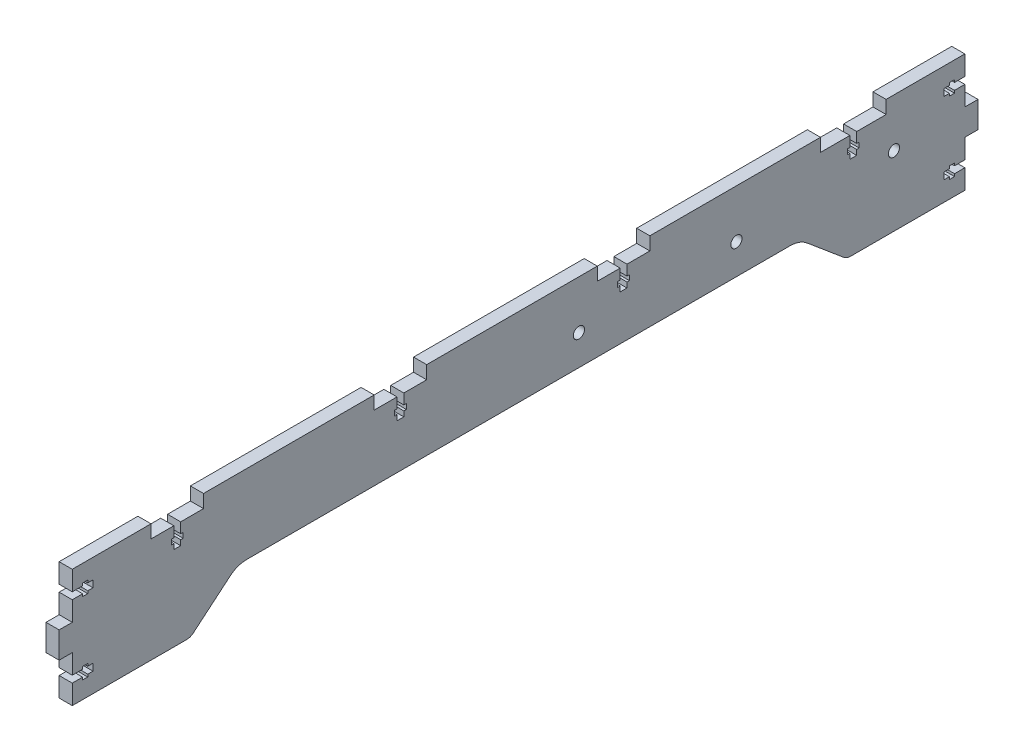
SolidWorks part; units mm, degrees
material "Pine"
ref_plane "Front Plane" through (0, 0, 0) normal (0, 0, 1) x (1, 0, 0)
ref_plane "Top Plane" through (0, 0, 0) normal (0, 1, 0) x (1, 0, 0)
ref_plane "Right Plane" through (0, 0, 0) normal (1, 0, 0) x (0, 0, -1)
sketch "Sketch1" plane through (0, 0, 0) normal (1, 0, 0) x (0, 0, -1)
  line L0 (-44.45, 57.15) -> (-44.45, 50.8)
  line L1 (-44.45, 50.8) -> (-55.5, 50.8)
  line L2 (-55.5, 50.8) -> (-55.5, 45.8)
  line L3 (-55.5, 45.8) -> (-54.3, 45.8)
  line L4 (-54.3, 45.8) -> (-54.3, 43.3)
  line L5 (-54.3, 43.3) -> (-55.5, 43.3)
  line L6 (-55.5, 43.3) -> (-55.5, 40.8)
  line L7 (-55.5, 40.8) -> (-58.8, 40.8)
  line L8 (-58.8, 40.8) -> (-58.8, 43.3)
  line L9 (-58.8, 43.3) -> (-60, 43.3)
  line L10 (-60, 43.3) -> (-60, 45.8)
  line L11 (-60, 45.8) -> (-58.8, 45.8)
  line L12 (-58.8, 45.8) -> (-58.8, 50.8)
  line L13 (-58.8, 50.8) -> (-69.85, 50.8)
  line L14 (-69.85, 50.8) -> (-69.85, 57.15)
  line L15 (-69.85, 57.15) -> (-152.4, 57.15)
  line L16 (-152.4, 57.15) -> (-152.4, 50.8)
  line L17 (-152.4, 50.8) -> (-163.45, 50.8)
  line L18 (-163.45, 50.8) -> (-163.45, 45.8)
  line L19 (-163.45, 45.8) -> (-162.25, 45.8)
  line L20 (-162.25, 45.8) -> (-162.25, 43.3)
  line L21 (-162.25, 43.3) -> (-163.45, 43.3)
  line L22 (-163.45, 43.3) -> (-163.45, 40.8)
  line L23 (-163.45, 40.8) -> (-166.75, 40.8)
  line L24 (-166.75, 40.8) -> (-166.75, 43.3)
  line L25 (-166.75, 43.3) -> (-167.95, 43.3)
  line L26 (-167.95, 43.3) -> (-167.95, 45.8)
  line L27 (-167.95, 45.8) -> (-166.75, 45.8)
  line L28 (-166.75, 45.8) -> (-166.75, 50.8)
  line L29 (-166.75, 50.8) -> (-177.8, 50.8)
  line L30 (-177.8, 50.8) -> (-177.8, 57.15)
  line L31 (-177.8, 57.15) -> (-215.9, 57.15)
  line L32 (-215.9, 57.15) -> (-215.9, 47.6875)
  line L33 (-215.9, 47.6875) -> (-210.9, 47.6875)
  line L34 (-210.9, 47.6875) -> (-210.9, 48.8875)
  line L35 (-210.9, 48.8875) -> (-208.4, 48.8875)
  line L36 (-208.4, 48.8875) -> (-208.4, 47.6875)
  line L37 (-208.4, 47.6875) -> (-205.9, 47.6875)
  line L38 (-205.9, 47.6875) -> (-205.9, 44.3875)
  line L39 (-205.9, 44.3875) -> (-208.4, 44.3875)
  line L40 (-208.4, 44.3875) -> (-208.4, 43.1875)
  line L41 (-208.4, 43.1875) -> (-210.9, 43.1875)
  line L42 (-210.9, 43.1875) -> (-210.9, 44.3875)
  line L43 (-210.9, 44.3875) -> (-215.9, 44.3875)
  line L44 (-215.9, 44.3875) -> (-215.9, 34.925)
  line L45 (-215.9, 34.925) -> (-222.25, 34.925)
  line L46 (-222.25, 34.925) -> (-222.25, 22.225)
  line L47 (-222.25, 22.225) -> (-215.9, 22.225)
  line L48 (-215.9, 22.225) -> (-215.9, 12.7625)
  line L49 (-215.9, 12.7625) -> (-210.9, 12.7625)
  line L50 (-210.9, 12.7625) -> (-210.9, 13.9625)
  line L51 (-210.9, 13.9625) -> (-208.4, 13.9625)
  line L52 (-208.4, 13.9625) -> (-208.4, 12.7625)
  line L53 (-208.4, 12.7625) -> (-205.9, 12.7625)
  line L54 (-205.9, 12.7625) -> (-205.9, 9.4625)
  line L55 (-205.9, 9.4625) -> (-208.4, 9.4625)
  line L56 (-208.4, 9.4625) -> (-208.4, 8.2625)
  line L57 (-208.4, 8.2625) -> (-210.9, 8.2625)
  line L58 (-210.9, 8.2625) -> (-210.9, 9.4625)
  line L59 (-210.9, 9.4625) -> (-215.9, 9.4625)
  line L60 (-215.9, 9.4625) -> (-215.9, 0)
  line L61 (-215.9, 0) -> (-160.599, 0)
  line L62 (-157.3336, 1.1885) -> (-139.5881, 16.0788)
  line L63 (-131.4247, 19.05) -> (131.4247, 19.05)
  line L64 (139.5881, 16.0788) -> (157.3336, 1.1885)
  line L65 (160.599, 0) -> (215.9, 0)
  line L66 (215.9, 0) -> (215.9, 9.4625)
  line L67 (215.9, 9.4625) -> (210.9, 9.4625)
  line L68 (210.9, 9.4625) -> (210.9, 8.2625)
  line L69 (210.9, 8.2625) -> (208.4, 8.2625)
  line L70 (208.4, 8.2625) -> (208.4, 9.4625)
  line L71 (208.4, 9.4625) -> (205.9, 9.4625)
  line L72 (205.9, 9.4625) -> (205.9, 12.7625)
  line L73 (205.9, 12.7625) -> (208.4, 12.7625)
  line L74 (208.4, 12.7625) -> (208.4, 13.9625)
  line L75 (208.4, 13.9625) -> (210.9, 13.9625)
  line L76 (210.9, 13.9625) -> (210.9, 12.7625)
  line L77 (210.9, 12.7625) -> (215.9, 12.7625)
  line L78 (215.9, 12.7625) -> (215.9, 22.225)
  line L79 (215.9, 22.225) -> (222.25, 22.225)
  line L80 (222.25, 22.225) -> (222.25, 34.925)
  line L81 (222.25, 34.925) -> (215.9, 34.925)
  line L82 (215.9, 34.925) -> (215.9, 44.3875)
  line L83 (215.9, 44.3875) -> (210.9, 44.3875)
  line L84 (210.9, 44.3875) -> (210.9, 43.1875)
  line L85 (210.9, 43.1875) -> (208.4, 43.1875)
  line L86 (208.4, 43.1875) -> (208.4, 44.3875)
  line L87 (208.4, 44.3875) -> (205.9, 44.3875)
  line L88 (205.9, 44.3875) -> (205.9, 47.6875)
  line L89 (205.9, 47.6875) -> (208.4, 47.6875)
  line L90 (208.4, 47.6875) -> (208.4, 48.8875)
  line L91 (208.4, 48.8875) -> (210.9, 48.8875)
  line L92 (210.9, 48.8875) -> (210.9, 47.6875)
  line L93 (210.9, 47.6875) -> (215.9, 47.6875)
  line L94 (215.9, 47.6875) -> (215.9, 57.15)
  line L95 (215.9, 57.15) -> (177.8, 57.15)
  line L96 (177.8, 57.15) -> (177.8, 50.8)
  line L97 (177.8, 50.8) -> (163.575, 50.8)
  line L98 (163.575, 50.8) -> (163.575, 45.8)
  line L99 (163.575, 45.8) -> (164.775, 45.8)
  line L100 (164.775, 45.8) -> (164.775, 43.3)
  line L101 (164.775, 43.3) -> (163.575, 43.3)
  line L102 (163.575, 43.3) -> (163.575, 40.8)
  line L103 (163.575, 40.8) -> (160.275, 40.8)
  line L104 (160.275, 50.8) -> (160.275, 45.8)
  line L105 (160.275, 43.3) -> (160.275, 40.8)
  line L106 (159.075, 43.3) -> (160.275, 43.3)
  line L107 (159.075, 45.8) -> (159.075, 43.3)
  line L108 (160.275, 45.8) -> (159.075, 45.8)
  line L109 (160.275, 50.8) -> (146.05, 50.8)
  line L110 (146.05, 50.8) -> (146.05, 57.15)
  line L111 (146.05, 57.15) -> (63.5, 57.15)
  line L112 (63.5, 57.15) -> (63.5, 50.8)
  line L113 (63.5, 50.8) -> (52.45, 50.8)
  line L114 (52.45, 50.8) -> (52.45, 45.8)
  line L115 (52.45, 45.8) -> (53.65, 45.8)
  line L116 (53.65, 45.8) -> (53.65, 43.3)
  line L117 (53.65, 43.3) -> (52.45, 43.3)
  line L118 (52.45, 43.3) -> (52.45, 40.8)
  line L119 (52.45, 40.8) -> (49.15, 40.8)
  line L120 (49.15, 40.8) -> (49.15, 43.3)
  line L121 (49.15, 43.3) -> (47.95, 43.3)
  line L122 (47.95, 43.3) -> (47.95, 45.8)
  line L123 (47.95, 45.8) -> (49.15, 45.8)
  line L124 (49.15, 45.8) -> (49.15, 50.8)
  line L125 (49.15, 50.8) -> (38.1, 50.8)
  line L126 (38.1, 50.8) -> (38.1, 57.15)
  line L127 (38.1, 57.15) -> (-44.45, 57.15)
  line L128 (177.8, 57.15) -> (146.05, 57.15) construction
  line L129 (161.925, 57.15) -> (161.925, 40.8) construction
  circle A0 centre (105.3883, 33.749) radius 2.7
  circle A2 centre (29.1883, 33.749) radius 2.7
  circle A3 centre (181.5883, 33.749) radius 2.7
  arc A4 (-160.599, 0) -> (-157.3336, 1.1885) centre (-160.599, 5.08) ccw
  arc A5 (-139.5881, 16.0788) -> (-131.4247, 19.05) centre (-131.4247, 6.35) cw
  arc A6 (131.4247, 19.05) -> (139.5881, 16.0788) centre (131.4247, 6.35) cw
  arc A7 (157.3336, 1.1885) -> (160.599, 0) centre (160.599, 5.08) ccw
  dimension "D13" = 5.08
  dimension "D14" = 12.7
  dimension "D17" = 5.08
  dimension "D18" = 12.7
  dimension "D1" = 152.4
  dimension "D2" = 76.2
  dimension "D3" = 23.401
  dimension "D4" = 34.3117
  dimension "D5" = 6.35
  dimension "D6" = 12.7
  dimension "D7" = 31.75
  dimension "D8" = 6.35
  dimension "D9" = 25.4
  dimension "D10" = 25.4
  dimension "D11" = 25.4
  dimension "D12" = 57.15
  dimension "D15" = 55.301
  dimension "D16" = 55.301
  dimension "D19" = 140
  dimension "D20" = 140
  dimension "D21" = 431.8
  dimension "D23" = 2.5
  dimension "D24" = 10
  dimension "D25" = 1.2
  dimension "D26" = 5
extrude "Boss-Extrude1" add sketch "Sketch1" against normal blind 6.35
